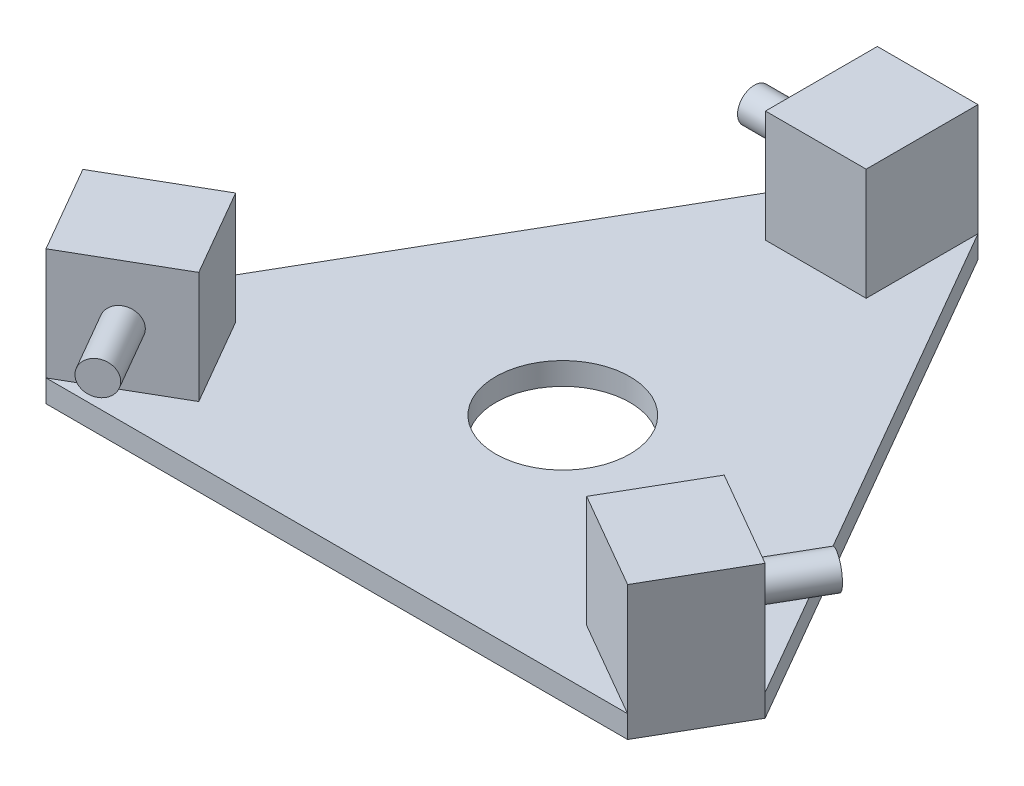
SolidWorks part; units mm, degrees
ref_plane "Front Plane" through (0, 0, 0) normal (0, 0, 1) x (1, 0, 0)
ref_plane "Top Plane" through (0, 0, 0) normal (0, 1, 0) x (1, 0, 0)
ref_plane "Right Plane" through (0, 0, 0) normal (1, 0, 0) x (0, 0, -1)
sketch "Sketch1" plane through (0, 0, 0) normal (0, 1, 0) x (1, 0, 0)
  line L0 (-152.5, -62.0652) -> (-130, -101.0363)
  line L1 (152.5, -62.0652) -> (22.5, 163.1015)
  line L2 (-22.5, 163.1015) -> (-152.5, -62.0652)
  line L3 (-130, -101.0363) -> (130, -101.0363)
  line L4 (-130, -101.0363) -> (-175, -101.0363) construction
  line L5 (-175, -101.0363) -> (-152.5, -62.0652) construction
  line L6 (130, -101.0363) -> (152.5, -62.0652)
  line L7 (22.5, 163.1015) -> (-22.5, 163.1015)
  line L8 (0, 202.0726) -> (-22.5, 163.1015) construction
  line L9 (0, 202.0726) -> (22.5, 163.1015) construction
  line L10 (175, -101.0363) -> (152.5, -62.0652) construction
  line L11 (175, -101.0363) -> (130, -101.0363) construction
  circle A0 centre (0, 0) radius 101.0363 construction
  circle A1 centre (0, 0) radius 30
  point P2 (175, -101.0363)
  point P3 (0, 202.0726)
  point P4 (-175, -101.0363)
  dimension "D3" = 60
  dimension "D1" = 350
  dimension "D2" = 45
extrude "Boss-Extrude1" add sketch "Sketch1" along normal blind 10
sketch "Sketch2" plane through (0, 10, 0) normal (0, 1, 0) x (1, 0, 0)
  line L0 (-22.5, 113.1015) -> (-22.5, 163.1015)
  line L1 (-22.5, 113.1015) -> (22.5, 113.1015)
  line L2 (-22.5, 163.1015) -> (22.5, 163.1015)
  line L3 (22.5, 113.1015) -> (22.5, 163.1015)
  line L4 (-22.5, 113.1015) -> (22.5, 163.1015) construction
  line L5 (-22.5, 163.1015) -> (22.5, 113.1015) construction
  line L6 (-86.6987, -76.0363) -> (-130, -101.0363)
  line L7 (-86.6987, -76.0363) -> (-109.1987, -37.0652)
  line L8 (-130, -101.0363) -> (-152.5, -62.0652)
  line L9 (-109.1987, -37.0652) -> (-152.5, -62.0652)
  line L10 (-86.6987, -76.0363) -> (-152.5, -62.0652) construction
  line L11 (-130, -101.0363) -> (-109.1987, -37.0652) construction
  line L12 (86.6987, -76.0363) -> (130, -101.0363)
  line L13 (86.6987, -76.0363) -> (109.1987, -37.0652)
  line L14 (130, -101.0363) -> (152.5, -62.0652)
  line L15 (109.1987, -37.0652) -> (152.5, -62.0652)
  line L16 (86.6987, -76.0363) -> (152.5, -62.0652) construction
  line L17 (130, -101.0363) -> (109.1987, -37.0652) construction
  point P1 (0, 138.1015)
  point P2 (-119.5994, -69.0507)
  point P3 (119.5994, -69.0507)
  dimension "D1" = 50
extrude "Boss-Extrude2" add sketch "Sketch2" along normal blind 50
sketch "Sketch3" plane through (-22.5, 0, -140.6015) normal (1, 0, 0) x (0, 0, -1)
  line L0 (22.5, 10) -> (-202.6666, 10) construction
  line L1 (-27.5, 10) -> (22.5, 10) construction
  line L2 (-27.5, 10) -> (-27.5, 60) construction
  line L3 (-27.5, 60) -> (22.5, 60) construction
  line L4 (22.5, 10) -> (22.5, 60) construction
  line L5 (-27.5, 10) -> (22.5, 60) construction
  line L6 (-27.5, 60) -> (22.5, 10) construction
  circle A0 centre (-2.5, 35) radius 7.5
  point P0 (-2.5, 35)
  dimension "D1" = 15
extrude "Boss-Extrude3" add sketch "Sketch3" against normal blind 30
sketch "Sketch4" plane through (133.0144, 0, 50.8152) normal (-0.5, 0, 0.866) x (0.866, 0, 0.5)
  line L0 (22.5, 10) -> (-202.6666, 10) construction
  line L1 (-27.5, 10) -> (22.5, 10) construction
  line L2 (-27.5, 10) -> (-27.5, 60) construction
  line L3 (-27.5, 60) -> (22.5, 60) construction
  line L4 (22.5, 10) -> (22.5, 60) construction
  line L5 (-27.5, 10) -> (22.5, 60) construction
  line L6 (-27.5, 60) -> (22.5, 10) construction
  circle A0 centre (-2.5, 35) radius 7.5
  point P0 (-2.5, 35)
  dimension "D1" = 15
extrude "Boss-Extrude4" add sketch "Sketch4" against normal blind 30
sketch "Sketch5" plane through (-110.5144, 0, 89.7863) normal (-0.5, 0, -0.866) x (-0.866, 0, 0.5)
  line L0 (22.5, 10) -> (-202.6666, 10) construction
  line L1 (-27.5, 10) -> (22.5, 10) construction
  line L2 (-27.5, 10) -> (-27.5, 60) construction
  line L3 (-27.5, 60) -> (22.5, 60) construction
  line L4 (22.5, 10) -> (22.5, 60) construction
  line L5 (-27.5, 10) -> (22.5, 60) construction
  line L6 (-27.5, 60) -> (22.5, 10) construction
  circle A0 centre (-2.5, 35) radius 7.5
  point P0 (-2.5, 35)
  dimension "D1" = 15
extrude "Boss-Extrude5" add sketch "Sketch5" against normal blind 30
